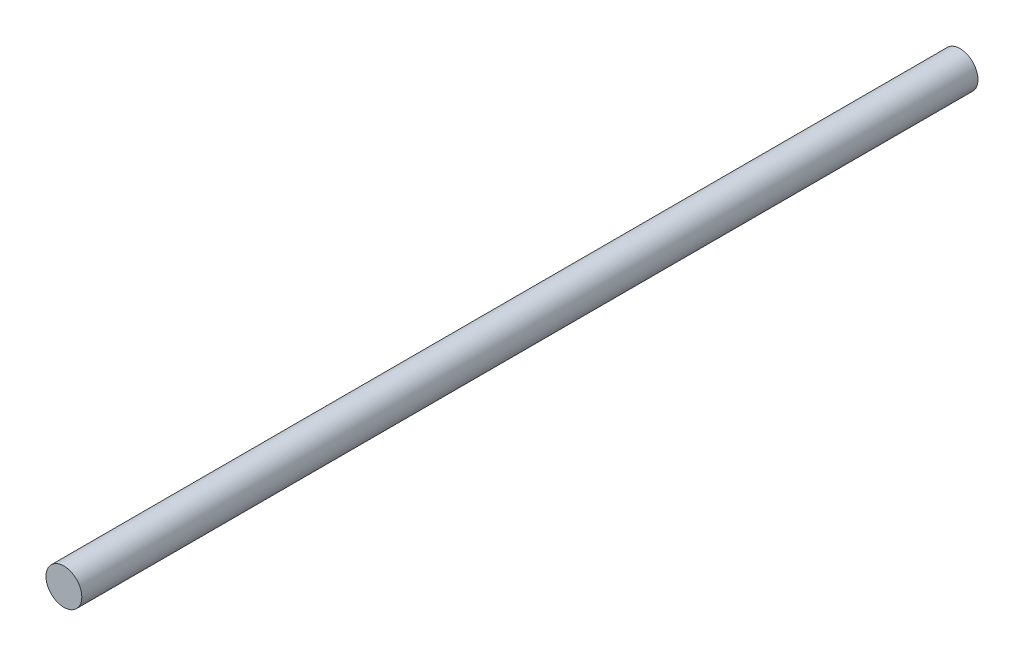
SolidWorks part; units mm, degrees
ref_plane "Front Plane" through (0, 0, 0) normal (0, 0, 1) x (1, 0, 0)
ref_plane "Top Plane" through (0, 0, 0) normal (0, 1, 0) x (1, 0, 0)
ref_plane "Right Plane" through (0, 0, 0) normal (1, 0, 0) x (0, 0, -1)
sketch "Sketch1" plane through (0, 0, 0) normal (0, 0, 1) x (1, 0, 0)
  circle A0 centre (0, 0) radius 10
  dimension "D1" = 20
extrude "Boss-Extrude1" add sketch "Sketch1" along normal mid plane 500
